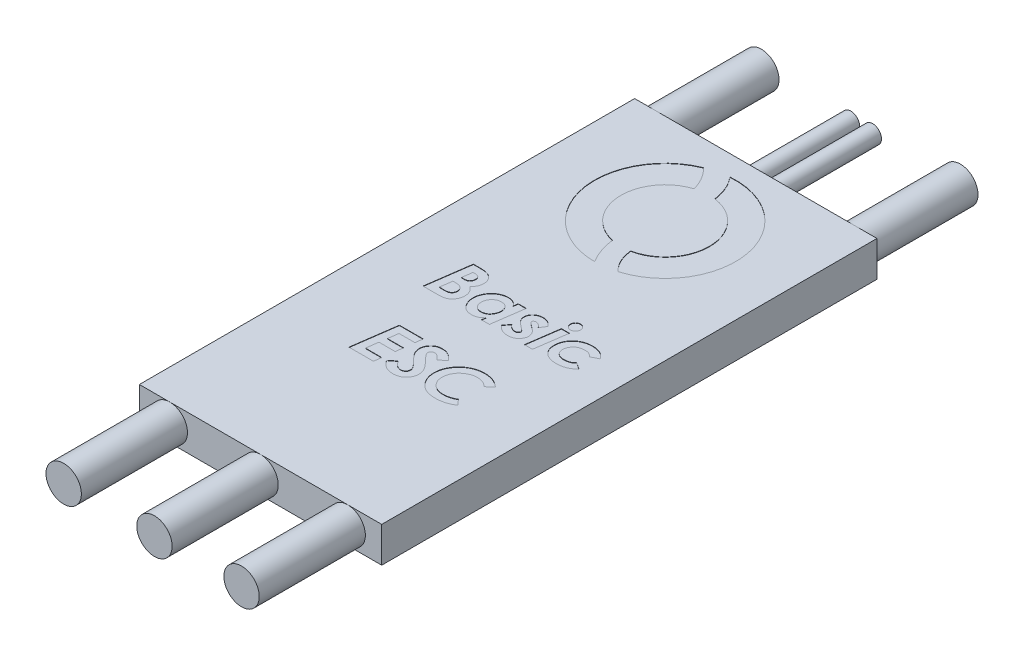
SolidWorks part; units mm, degrees
ref_plane "Front Plane" through (0, 0, 0) normal (0, 0, 1) x (1, 0, 0)
ref_plane "Top Plane" through (0, 0, 0) normal (0, 1, 0) x (1, 0, 0)
ref_plane "Right Plane" through (0, 0, 0) normal (1, 0, 0) x (0, 0, -1)
sketch "Sketch1" plane through (0, 0, 0) normal (0, 1, 0) x (1, 0, 0)
  line L1 (8.6995, 17.78) -> (-8.6995, 17.78)
  line L2 (8.6995, 17.78) -> (8.6995, -17.78)
  line L3 (8.6995, -17.78) -> (-8.6995, -17.78)
  line L4 (-8.6995, 17.78) -> (-8.6995, -17.78)
  line L5 (8.6995, 17.78) -> (-8.6995, -17.78) construction
  line L6 (8.6995, -17.78) -> (-8.6995, 17.78) construction
  point P0 (0, 0)
  dimension "D1" = 17.399
  dimension "D2" = 35.56
extrude "Boss-Extrude1" add sketch "Sketch1" along normal blind 2.54
sketch "Sketch3" plane through (0, 0, 17.78) normal (0, 0, 1) x (1, 0, 0)
  circle A0 centre (6.2551, 1.27) radius 1.27
  circle A1 centre (0, 1.27) radius 1.27
  circle A2 centre (-6.5163, 1.27) radius 1.27
  dimension "D1" = 2.54
  dimension "D2" = 2.54
  dimension "D3" = 2.54
extrude "Boss-Extrude2" add sketch "Sketch3" along normal blind 7.62
sketch "Sketch4" plane through (0, 0, -17.78) normal (0, 0, -1) x (-1, 0, 0)
  circle A0 centre (-7.0647, 1.27) radius 1.27
  circle A1 centre (7.2215, 1.27) radius 1.27
  circle A2 centre (-0.7705, 1.27) radius 0.635
  circle A3 centre (0.7966, 1.27) radius 0.635
  dimension "D1" = 2.54
  dimension "D2" = 2.54
  dimension "D3" = 1.27
  dimension "D4" = 1.27
extrude "Boss-Extrude3" add sketch "Sketch4" along normal blind 7.62
sketch "Sketch5" plane through (0, 2.54, 0) normal (0, 1, 0) x (1, 0, 0)
  arc A0 (-1.9303, 15.9583) -> (0, 6.2024) centre (0, 11.2713) ccw
  arc A1 (-0.948, 14.3019) -> (-0.683, 8.1703) centre (0, 11.2713) ccw
  arc A2 (1.4658, 6.419) -> (-0.4001, 16.3244) centre (0, 11.2713) ccw
  arc A3 (0.636, 8.1603) -> (0.4197, 14.4188) centre (0, 11.2713) ccw
  spline S0 degree 2 poles (0.4197, 14.4188) (0.2754, 15.5127) (-0.4001, 16.3244) knots 0 0 0 1 1 1
  spline S1 degree 2 poles (-0.948, 14.3019) (-1.2235, 15.2805) (-1.9303, 15.9583) knots 0 0 0 1 1 1
  spline S2 degree 2 poles (-0.683, 8.1703) (-0.5501, 7.0975) (0, 6.2024) knots 0 0 0 1 1 1
  spline S3 degree 2 poles (0.636, 8.1603) (0.7428, 7.1076) (1.4658, 6.419) knots 0 0 0 1 1 1
  text T0 "<b><i>Basic </i></b>\r\n<b><i> ESC</i></b>" font "Century Gothic" height 3.175
extrude "Cut-Extrude1" cut sketch "Sketch5" against normal blind 0.0254
